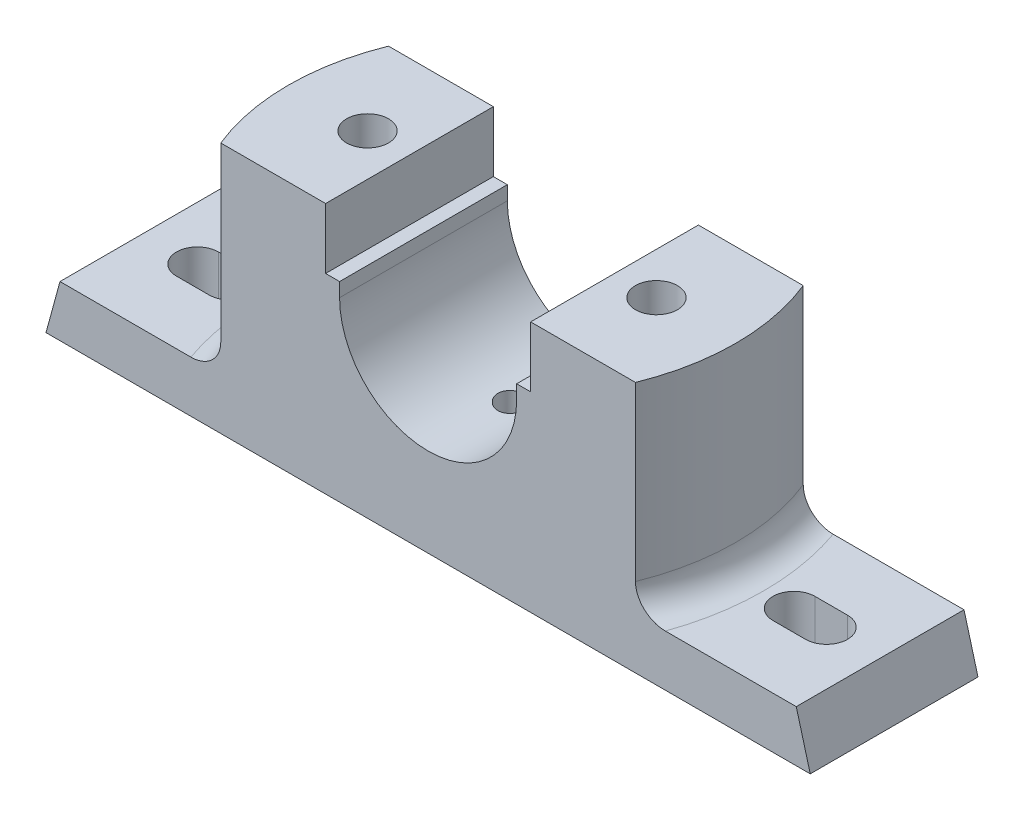
SolidWorks part; units mm, degrees
ref_plane "Front Plane" through (0, 0, 0) normal (0, 0, 1) x (1, 0, 0)
ref_plane "Top Plane" through (0, 0, 0) normal (0, 1, 0) x (1, 0, 0)
ref_plane "Right Plane" through (0, 0, 0) normal (1, 0, 0) x (0, 0, -1)
sketch "Sketch1" plane through (0, 0, 0) normal (0, 0, 1) x (1, 0, 0)
  line L0 (0, 57.1369) -> (0, -64.9031) construction
  line L1 (-82, -43.8235) -> (82, -43.8235)
  line L2 (82, -43.8235) -> (79, -32.8235)
  line L3 (79, -32.8235) -> (50, -32.8235)
  line L4 (50, -32.8235) -> (50, 10.1765)
  line L5 (50, 10.1765) -> (22, 10.1765)
  line L6 (22, 10.1765) -> (22, -2.8235)
  line L7 (22, -2.8235) -> (19, -2.8235)
  line L8 (19, -2.8235) -> (19, -5.8235)
  line L9 (-82, -43.8235) -> (-79, -32.8235)
  line L10 (-79, -32.8235) -> (-50, -32.8235)
  line L11 (-50, -32.8235) -> (-50, 10.1765)
  line L12 (-50, 10.1765) -> (-22, 10.1765)
  line L13 (-22, 10.1765) -> (-22, -2.8235)
  line L14 (-22, -2.8235) -> (-19, -2.8235)
  line L15 (-19, -2.8235) -> (-19, -5.8235)
  arc A0 (19, -5.8235) -> (-19, -5.8235) centre (0, -5.8235) cw
  point P5 (0, -5.8235)
  point P16 (0, -43.8235)
  dimension "D1" = 3
  dimension "D2" = 11
  dimension "D3" = 164
  dimension "D4" = 0
  dimension "D5" = 38
  dimension "D6" = 100
  dimension "D7" = 44
  dimension "D8" = 3
  dimension "D9" = 16
  dimension "D10" = 54
extrude "Boss-Extrude3" add sketch "Sketch1" along normal mid plane 36
sketch "Sketch3" plane through (0, 10.1765, 0) normal (0, 1, 0) x (1, 0, 0)
  line L4 (-22, 18) -> (-50, 18)
  line L5 (-50, 18) -> (-50, -18)
  line L6 (-50, -18) -> (-22, -18)
  line L7 (-22, -18) -> (-22, 18)
  line L8 (-44.4972, 18) -> (-50, 18)
  line L9 (-50, 18) -> (-50, -18)
  line L10 (-50, -18) -> (-44.4972, -18)
  arc A0 (-44.4972, 18) -> (-44.4972, -18) centre (0, 0) ccw
  dimension "D2" = 48
  dimension "D1" = 0
extrude "Cut-Extrude1" cut sketch "Sketch3" against normal up to surface (43 mm away) up to face at (-64.5, -32.8235, 0)
mirror "Mirror1" about plane through (0, 0, 0) normal (1, 0, 0) of "Cut-Extrude1"
hole_wizard "Ø8.0mm Dowel Hole1" positions "3DSketch2" profile "Sketch5" hole size "Ø8.0" standard "ISO"
sketch3d "3DSketch2"
  point P0 (0, -24.8235, 0)
  dimension "D1" = 0
  dimension "D2" = 0
sketch "Sketch5" plane through (0, -24.8235, 0) normal (1, 0, 0) x (0, 0, 1)
  line L0 (0, 0) -> (0, 7.8026)
  line L1 (0, 7.8026) -> (3, 6)
  line L2 (3, 6) -> (3, 0)
  line L5 (3, 0) -> (0, 0)
  line L10 (0, 7.8026) -> (-3, 6) construction
  line L11 (0, -6.35) -> (0, 107.95) construction
  dimension "Hole Dia." = 6
  dimension "Hole Depth" = 6
  dimension "Drill Angle" = 118
hole_wizard "M10 Tapped Hole1" positions "Sketch7" profile "Sketch8" tap size "M10" standard "ISO" end condition through all
sketch "Sketch7" plane through (0, 10.1765, 0) normal (0, 1, 0) x (1, 0, 0)
  line L0 (0, -19.8) -> (0, 19.8) construction
  point P0 (-31, 0)
  dimension "D1" = 31
sketch "Sketch8" plane through (-31, 10.1765, 0) normal (1, 0, 0) x (0, 0, 1)
  line L0 (0, 0) -> (0, 54)
  line L1 (0, 54) -> (4.5, 54)
  line L2 (4.5, 54) -> (4.5, 0)
  line L5 (4.5, 0) -> (0, 0)
  line L11 (0, -6.35) -> (0, 107.95) construction
  dimension "Thru Tap Drill Dia." = 9
  dimension "Thru Tap Drill Depth" = 54
cosmetic thread "Hole Thread2" parameters "D2"=10
sketch "Sketch9" plane through (0, -43.8235, 0) normal (0, -1, 0) x (1, 0, 0)
  line L1 (-41, 10) -> (-21, 10)
  line L2 (-41, 10) -> (-41, -10)
  line L3 (-41, -10) -> (-21, -10)
  line L4 (-21, 10) -> (-21, -10)
  line L5 (-41, 10) -> (-21, -10) construction
  line L6 (-41, -10) -> (-21, 10) construction
  point P0 (-31, 0)
  dimension "D1" = 20
extrude "Cut-Extrude2" cut sketch "Sketch9" against normal blind 8
sketch "Sketch10" plane through (0, -43.8235, 0) normal (0, -1, 0) x (1, 0, 0)
  line L0 (-67.5, 0) -> (-60.5, 0) construction
  line L1 (-67.5, 4.5) -> (-60.5, 4.5)
  line L2 (-67.5, -4.5) -> (-60.5, -4.5)
  arc A0 (-67.5, 4.5) -> (-67.5, -4.5) centre (-67.5, 0) ccw
  arc A1 (-60.5, -4.5) -> (-60.5, 4.5) centre (-60.5, 0) ccw
  point P2 (-64, 0)
  dimension "D1" = 16
  dimension "D2" = 9
  dimension "D3" = 64
extrude "Cut-Extrude3" cut sketch "Sketch10" against normal up to next (11 mm away)
mirror "Mirror2" about plane through (0, 0, 0) normal (1, 0, 0) of "Cut-Extrude3", "Cut-Extrude2", "M10 Tapped Hole1"
fillet "Fillet2" radius 6 1 edges at (-48, -32.8235, 0)
fillet "Fillet3" radius 6 1 edges at (48, -32.8235, 0)
